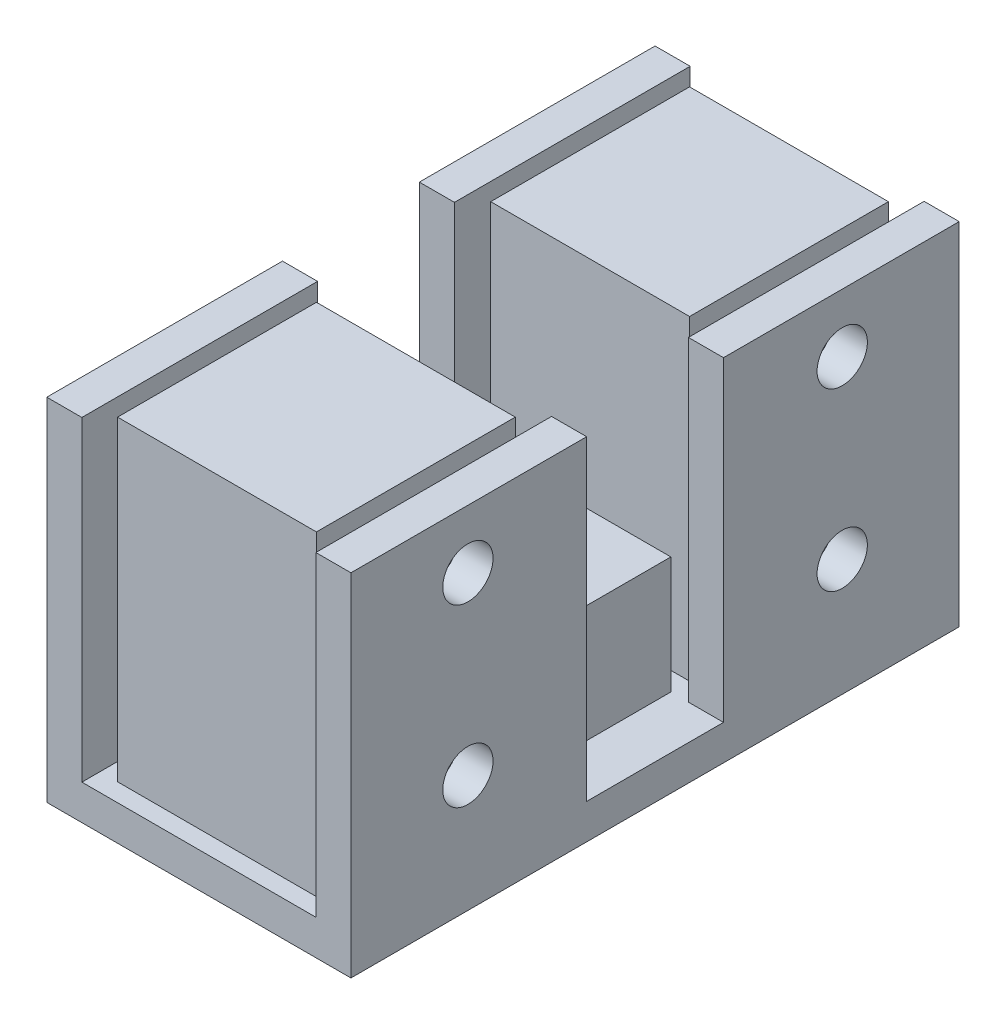
SolidWorks part; units mm, degrees
ref_plane "Front Plane" through (0, 0, 0) normal (0, 0, 1) x (1, 0, 0)
ref_plane "Top Plane" through (0, 0, 0) normal (0, 1, 0) x (1, 0, 0)
ref_plane "Right Plane" through (0, 0, 0) normal (1, 0, 0) x (0, 0, -1)
sketch "Sketch1" plane through (0, 0, 0) normal (0, 1, 0) x (1, 0, 0)
  line L1 (0, 0) -> (26, 0)
  line L2 (0, 0) -> (0, 52)
  line L3 (0, 52) -> (26, 52)
  line L4 (26, 0) -> (26, 52)
  dimension "D1" = 52
  dimension "D2" = 26
extrude "Boss-Extrude1" add sketch "Sketch1" along normal blind 30
sketch "Sketch2" plane through (0, 0, -52) normal (0, 0, -1) x (-1, 0, 0)
  line L0 (-26, 30) -> (0, 30) construction
  line L1 (-23, 30) -> (-21.5, 30)
  line L2 (-23, 30) -> (-23, 3)
  line L3 (-23, 3) -> (-21.5, 3)
  line L4 (-21.5, 30) -> (-21.5, 3)
  line L5 (-26, 30) -> (-26, 0) construction
  line L6 (-4.5, 30) -> (-3, 30)
  line L7 (-4.5, 30) -> (-4.5, 3)
  line L8 (-4.5, 3) -> (-3, 3)
  line L9 (-3, 30) -> (-3, 3)
  line L10 (0, 30) -> (0, 0) construction
  line L11 (-26, 0) -> (0, 0) construction
  dimension "D1" = 17
  dimension "D2" = 3
  dimension "D3" = 3
  dimension "D4" = 3
extrude "Cut-Extrude1" cut sketch "Sketch2" against normal through all
sketch "Sketch3" plane through (0, 30, 0) normal (0, 1, 0) x (1, 0, 0)
  line L0 (4.5, 31.85) -> (4.5, 20.15)
  line L2 (4.5, 50.45) -> (4.5, 33.45)
  line L4 (21.5, 50.45) -> (21.5, 33.45)
  line L5 (4.5, 50.45) -> (21.5, 50.45)
  line L6 (4.5, 50.45) -> (4.5, 33.45)
  line L7 (4.5, 33.45) -> (21.5, 33.45)
  line L8 (21.5, 50.45) -> (21.5, 33.45)
  line L9 (4.5, 18.55) -> (21.5, 18.55)
  line L10 (4.5, 18.55) -> (4.5, 1.55)
  line L11 (4.5, 1.55) -> (21.5, 1.55)
  line L12 (21.5, 18.55) -> (21.5, 1.55)
  line L13 (4.5, 31.85) -> (21.5, 31.85)
  line L14 (4.5, 31.85) -> (4.5, 20.15)
  line L15 (4.5, 20.15) -> (21.5, 20.15)
  line L16 (21.5, 31.85) -> (21.5, 20.15)
  line L17 (21.5, 31.85) -> (21.5, 20.15)
  line L18 (4.5, 18.55) -> (4.5, 1.55)
  line L19 (21.5, 18.55) -> (21.5, 1.55)
  line L20 (21.5, 52) -> (4.5, 52) construction
  line L21 (4.5, 0) -> (4.5, 52) construction
  line L22 (21.5, 0) -> (21.5, 52) construction
  line L23 (4.5, 0) -> (21.5, 0) construction
  line L24 (3, 0) -> (3, 52) construction
  line L25 (0, 52) -> (3, 52)
  line L26 (0, 52) -> (0, 31.85)
  line L27 (0, 31.85) -> (3, 31.85)
  line L28 (3, 52) -> (3, 31.85)
  line L29 (23, 0) -> (23, 52) construction
  line L30 (26, 52) -> (23, 52)
  line L31 (26, 52) -> (26, 31.85)
  line L32 (26, 31.85) -> (23, 31.85)
  line L33 (23, 52) -> (23, 31.85)
  line L35 (0, 0) -> (3, 0)
  line L36 (0, 0) -> (0, 20.15)
  line L37 (0, 20.15) -> (3, 20.15)
  line L38 (3, 0) -> (3, 20.15)
  line L39 (23, 20.15) -> (26, 20.15)
  line L40 (23, 20.15) -> (23, 0)
  line L41 (23, 0) -> (26, 0)
  line L42 (26, 20.15) -> (26, 0)
  line M18 (21.5, 0) -> (21.5, 52)
  line M20 (4.5, 52) -> (4.5, 0)
  dimension "D1" = 17
  dimension "D2" = 17
  dimension "D3" = 1.55
  dimension "D4" = 1.55
  dimension "D5" = 1.6
  dimension "D6" = 1.6
extrude "Cut-Extrude2" cut sketch "Sketch3" against normal up to surface (27 mm away) flip side to cut contours L7 L5 M20 M18 | L15 L13 M20 M18 | L11 L9 M20 M18 | L26 L25 L28 L27 | L31 L30 L33 L32 | L36 L35 L38 L37 | L40 L39 L42 L41 up to face at (3.75, 3, -26)
sketch "Sketch4" plane through (0, 30, 0) normal (0, 1, 0) x (1, 0, 0)
  line L4 (4.5, 20.15) -> (21.5, 20.15)
  line L5 (21.5, 20.15) -> (21.5, 31.85)
  line L6 (21.5, 31.85) -> (4.5, 31.85)
  line L7 (4.5, 31.85) -> (4.5, 20.15)
  line L8 (4.5, 20.15) -> (21.5, 20.15)
  line L9 (21.5, 20.15) -> (21.5, 31.85)
  line L10 (21.5, 31.85) -> (4.5, 31.85)
  line L11 (4.5, 31.85) -> (4.5, 20.15)
  dimension "D1" = 0
extrude "Cut-Extrude3" cut sketch "Sketch4" against normal offset from surface (17 mm away) 10 up to face at (13, 3, -10.05)
sketch "Sketch5" plane through (0, 0, 0) normal (-1, 0, 0) x (0, 0, 1)
  line L0 (-52, 30) -> (-52, 0) construction
  line L1 (-52, 30) -> (-31.85, 30) construction
  line L2 (0, 30) -> (0, 0) construction
  circle A0 centre (-42, 25) radius 2.15
  circle A1 centre (-42, 10) radius 2.15
  circle A2 centre (-10, 25) radius 2.15
  circle A3 centre (-10, 10) radius 2.15
  dimension "D1" = 4.3
  dimension "D2" = 10
  dimension "D3" = 15
  dimension "D4" = 5
  dimension "D5" = 10
extrude "Cut-Extrude4" cut sketch "Sketch5" against normal through all
